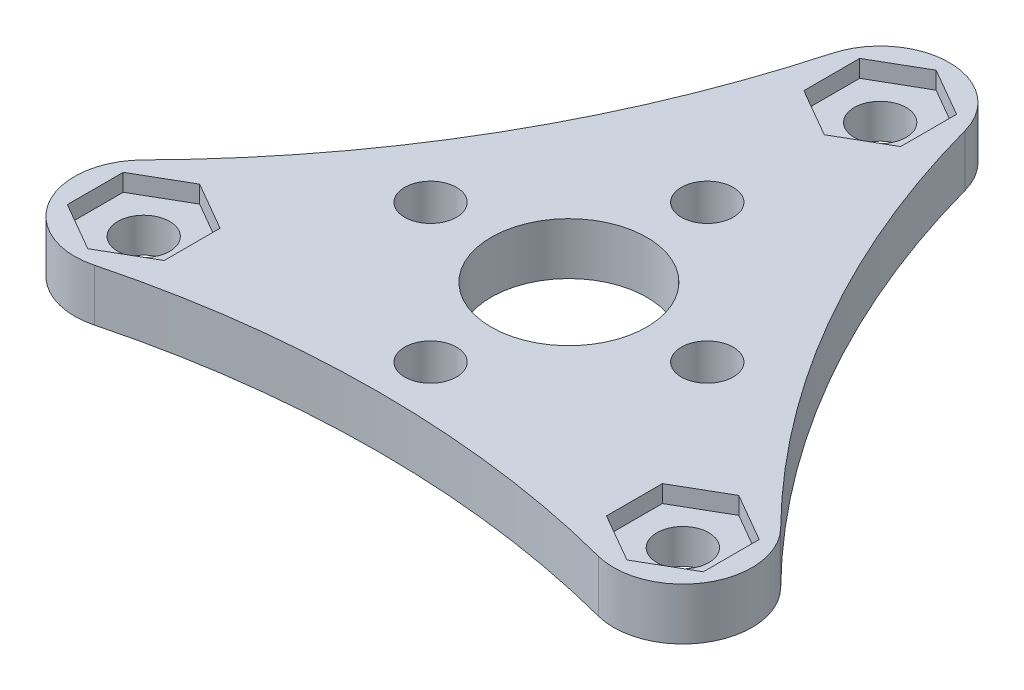
SolidWorks part; units mm, degrees
ref_plane "前视基准面" through (0, 0, 0) normal (0, 0, 1) x (1, 0, 0)
ref_plane "上视基准面" through (0, 0, 0) normal (0, 1, 0) x (1, 0, 0)
ref_plane "右视基准面" through (0, 0, 0) normal (1, 0, 0) x (0, 0, -1)
sketch "草图1" plane through (0, 0, 0) normal (0, 1, 0) x (1, 0, 0)
  line L0 (0, -8) -> (0, -11) construction
  circle A0 centre (0, 0) radius 8 construction
  circle A1 centre (8, 0) radius 1.5
  circle A2 centre (0, -8) radius 1.5
  circle A3 centre (-8, 0) radius 1.5
  circle A4 centre (0, 8) radius 1.5
  circle A5 centre (0, 18) radius 1.5
  circle A7 centre (15.5885, -9) radius 1.5
  circle A9 centre (-15.5885, -9) radius 1.5
  circle A11 centre (0, -18) radius 1.5 [skipped]
  circle A12 centre (-15.5885, 9) radius 1.5 [skipped]
  circle A13 centre (15.5885, 9) radius 1.5 [skipped]
  arc A14 (3.857, 19.06) -> (-3.857, 19.06) centre (0, 18) ccw
  arc A15 (-18.4349, -6.1897) -> (-14.5779, -12.8703) centre (-15.5885, -9) ccw
  arc A16 (14.5779, -12.8703) -> (18.4349, -6.1897) centre (15.5885, -9) ccw
  circle A17 centre (0, 0) radius 4.5
  arc A18 (-18.4349, -6.1897) -> (-3.857, 19.06) centre (-59.4992, 34.3519) ccw
  arc A19 (3.857, 19.06) -> (18.4349, -6.1897) centre (59.4992, 34.3519) ccw
  arc A20 (14.5779, -12.8703) -> (-14.5779, -12.8703) centre (0, -68.7038) ccw
  point P14 (0, 0)
  point P26 (0, 0)
  point P39 (0, 0)
  point P43 (0, 0)
  dimension "D1" = 16
  dimension "D2" = 3
  dimension "D4" = 3
  dimension "D5" = 18
  dimension "D9" = 8
  dimension "D11" = 9
  dimension "D12" = 3
  dimension "D10" = 3
  dimension "D3" = 4
  dimension "D6" = 6
extrude "凸台-拉伸1" add sketch "草图1" along normal blind 3
sketch "草图2" plane through (0, 3, 0) normal (0, 1, 0) x (1, 0, 0)
  line L1 (0, 14.7668) -> (2.8, 16.3834)
  line L2 (2.8, 16.3834) -> (2.8, 19.6166)
  line L3 (2.8, 19.6166) -> (0, 21.2332)
  line L4 (0, 21.2332) -> (-2.8, 19.6166)
  line L5 (-2.8, 19.6166) -> (-2.8, 16.3834)
  line L6 (-2.8, 16.3834) -> (0, 14.7668)
  line L12 (12.7885, -7.3834) -> (12.7885, -10.6166)
  line L13 (12.7885, -10.6166) -> (15.5885, -12.2332)
  line L14 (15.5885, -12.2332) -> (18.3885, -10.6166)
  line L15 (18.3885, -10.6166) -> (18.3885, -7.3834)
  line L16 (18.3885, -7.3834) -> (15.5885, -5.7668)
  line L17 (15.5885, -5.7668) -> (12.7885, -7.3834)
  line L24 (-12.7885, -7.3834) -> (-15.5885, -5.7668)
  line L25 (-15.5885, -5.7668) -> (-18.3885, -7.3834)
  line L26 (-18.3885, -7.3834) -> (-18.3885, -10.6166)
  line L27 (-18.3885, -10.6166) -> (-15.5885, -12.2332)
  line L28 (-15.5885, -12.2332) -> (-12.7885, -10.6166)
  line L29 (-12.7885, -10.6166) -> (-12.7885, -7.3834)
  line L36 (-12.7885, 7.3834) -> (-12.7885, 10.6166) [skipped]
  line L37 (-12.7885, 10.6166) -> (-15.5885, 12.2332) [skipped]
  line L38 (-15.5885, 12.2332) -> (-18.3885, 10.6166) [skipped]
  line L39 (-18.3885, 10.6166) -> (-18.3885, 7.3834) [skipped]
  line L40 (-18.3885, 7.3834) -> (-15.5885, 5.7668) [skipped]
  line L41 (-15.5885, 5.7668) -> (-12.7885, 7.3834) [skipped]
  line L42 (12.7885, 7.3834) -> (15.5885, 5.7668) [skipped]
  line L43 (15.5885, 5.7668) -> (18.3885, 7.3834) [skipped]
  line L44 (18.3885, 7.3834) -> (18.3885, 10.6166) [skipped]
  line L45 (18.3885, 10.6166) -> (15.5885, 12.2332) [skipped]
  line L46 (15.5885, 12.2332) -> (12.7885, 10.6166) [skipped]
  line L47 (12.7885, 10.6166) -> (12.7885, 7.3834) [skipped]
  line L48 (0, -14.7668) -> (-2.8, -16.3834) [skipped]
  line L49 (-2.8, -16.3834) -> (-2.8, -19.6166) [skipped]
  line L50 (-2.8, -19.6166) -> (0, -21.2332) [skipped]
  line L51 (0, -21.2332) -> (2.8, -19.6166) [skipped]
  line L52 (2.8, -19.6166) -> (2.8, -16.3834) [skipped]
  line L53 (2.8, -16.3834) -> (0, -14.7668) [skipped]
  circle A0 centre (0, 18) radius 2.8 construction
  point P41 (0, 0)
  dimension "D1" = 5.6
  dimension "D2" = 6
extrude "切除-拉伸1" cut sketch "草图2" against normal blind 1
